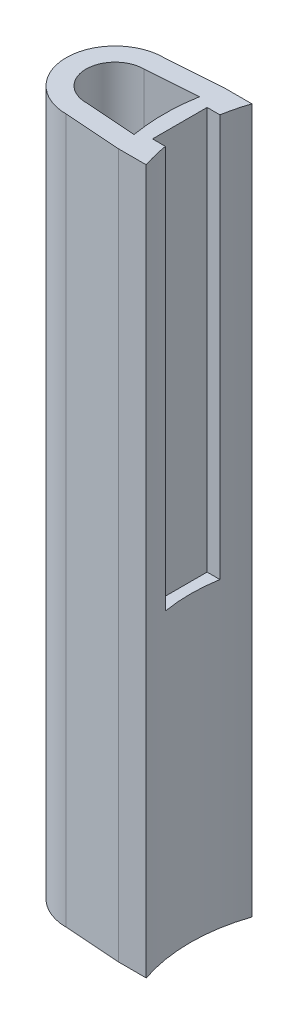
SolidWorks part; units mm, degrees
ref_plane "Front Plane" through (0, 0, 0) normal (0, 0, 1) x (1, 0, 0)
ref_plane "Top Plane" through (0, 0, 0) normal (0, 1, 0) x (1, 0, 0)
ref_plane "Right Plane" through (0, 0, 0) normal (1, 0, 0) x (0, 0, -1)
sketch "Sketch2" plane through (0, 0, 0) normal (0, 1, 0) x (1, 0, 0)
  line L0 (0, 2.775) -> (3.198, 3)
  line L1 (0, -2.775) -> (3.198, -3)
  line L2 (3.198, -3) -> (4.7694, -3)
  line L3 (3.198, 3) -> (4.7694, 3)
  line L4 (0, 1.65) -> (2.935, 1.8565)
  line L5 (0, -1.65) -> (2.935, -1.8565)
  arc A0 (0, 1.65) -> (0, -1.65) centre (0, 0) ccw
  arc A1 (0, 2.775) -> (0, -2.775) centre (0, 0) ccw
  arc A2 (2.935, 1.8565) -> (2.935, -1.8565) centre (13.625, 0) ccw
  arc A3 (4.7694, 3) -> (4.7694, -3) centre (13.625, 0) ccw
  arc A4 (4.7694, -3) -> (4.7694, 3) centre (13.625, 0) ccw construction
  arc A5 (3.198, -3) -> (3.198, 3) centre (13.625, 0) ccw construction
  arc A6 (2.935, -1.8565) -> (3.198, -3) centre (13.625, 0) ccw construction
  arc A7 (3.198, 3) -> (2.935, 1.8565) centre (13.625, 0) ccw construction
  arc A8 (0, -1.65) -> (0, 1.65) centre (0, 0) ccw construction
  arc A9 (2.775, 0) -> (2.1131, 1.7987) centre (0, 0) ccw construction
  arc A10 (2.1131, -1.7987) -> (2.775, 0) centre (0, 0) ccw construction
  arc A11 (0, -2.775) -> (2.1131, -1.7987) centre (0, 0) ccw construction
  arc A12 (2.1131, 1.7987) -> (0, 2.775) centre (0, 0) ccw construction
  point P9 (2.775, 0)
  dimension "D1" = 3.3
  dimension "D2" = 5.55
  dimension "D3" = 21.7
  dimension "D4" = 18.7
  dimension "D5" = 3
  dimension "D6" = 3
extrude "Boss-Extrude1" add sketch "Sketch2" along normal blind 40
sketch "Sketch3" plane through (0, 40, 0) normal (0, 1, 0) x (1, 0, 0)
  line L0 (4.4044, 1.55) -> (4.875, 1.55) construction
  line L1 (3.675, 1.55) -> (4.4044, 1.55)
  line L2 (3.675, 1.55) -> (3.675, -1.55)
  line L3 (3.675, -1.55) -> (4.4044, -1.55)
  line L4 (4.875, 1.55) -> (4.875, -1.55) construction
  line L5 (3.675, 1.55) -> (4.875, -1.55) construction
  line L6 (3.675, -1.55) -> (4.875, 1.55) construction
  line L7 (4.4044, -1.55) -> (4.875, -1.55) construction
  arc A0 (4.7694, 3) -> (4.7694, -3) centre (13.625, 0) ccw construction
  arc A1 (4.4044, 1.55) -> (4.4044, -1.55) centre (13.625, 0) ccw
  arc A2 (4.7694, 3) -> (4.4044, 1.55) centre (13.625, 0) ccw construction
  arc A3 (4.4044, -1.55) -> (4.7694, -3) centre (13.625, 0) ccw construction
  point P3 (4.275, 0)
  dimension "D1" = 3.1
  dimension "D2" = 0.6
extrude "Cut-Extrude1" cut sketch "Sketch3" against normal blind 22.8571
equation "\"ROD_OD\"= 3.25mm"
equation "\"ID\"= \"ROD_OD\" + 0.05mm'OF LUG"
equation "\"OD\"= \"ID\" + 2.25mm"
equation "\"BW\"= 6mm'LUG BASE WIDTH"
equation "\"BL\"= 40mm'LUG BASE LENGTH"
equation "\"ROCKET_OD\"= 18.7mm"
equation "\"D1@Sketch2\"=\"ID\""
equation "\"D2@Sketch2\"=\"OD\""
equation "\"D3@Sketch2\"=\"ROCKET_OD\"+3MM"
equation "\"D4@Sketch2\"=\"ROCKET_OD\""
equation "\"D5@Sketch2\"=\"BW\"/2"
equation "\"D6@Sketch2\"=\"BW\"/2"
equation "\"D1@Boss-Extrude1\"=\"BL\""
equation "\"D1@Cut-Extrude1\"=\"BL\"*4/7"
